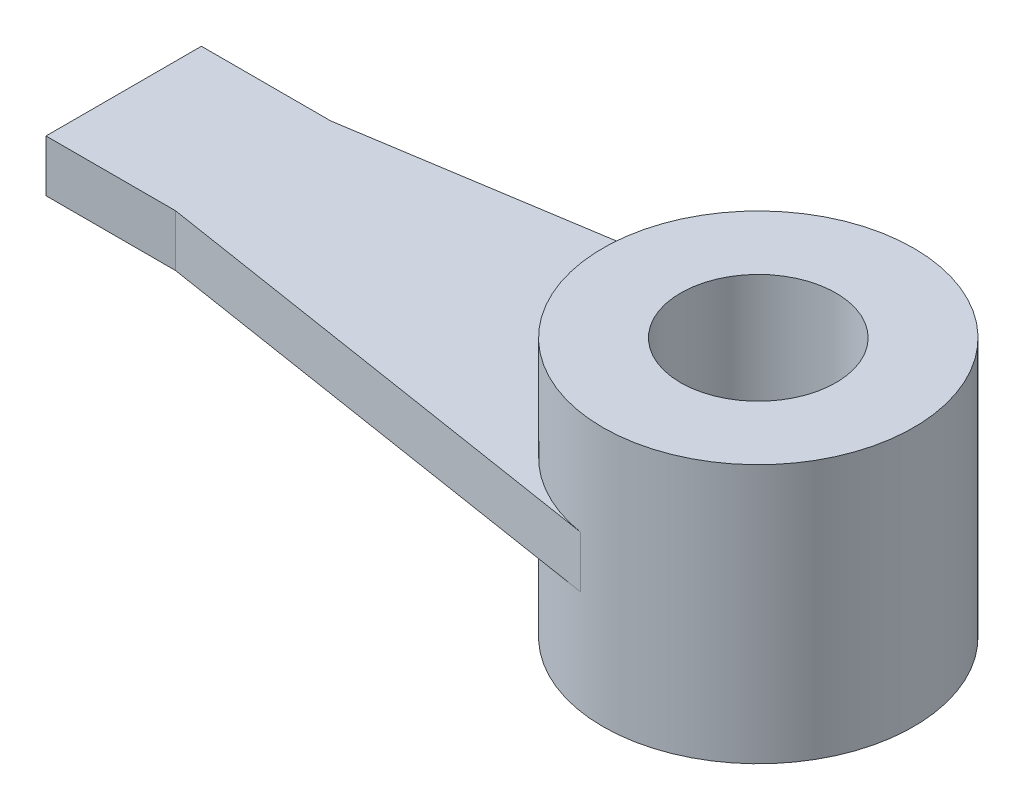
SolidWorks part; units mm, degrees
ref_plane "Front Plane" through (0, 0, 0) normal (0, 0, 1) x (1, 0, 0)
ref_plane "Top Plane" through (0, 0, 0) normal (0, 1, 0) x (1, 0, 0)
ref_plane "Right Plane" through (0, 0, 0) normal (1, 0, 0) x (0, 0, -1)
sketch "Sketch1" plane through (0, 0, 0) normal (0, 1, 0) x (1, 0, 0)
  circle A0 centre (0, 0) radius 15
  circle A1 centre (0, 0) radius 30
  dimension "D1" = 60
  dimension "D2" = 30
extrude "Boss-Extrude1" add sketch "Sketch1" along normal mid plane 50
sketch "Sketch2" plane through (0, 0, 0) normal (0, 1, 0) x (1, 0, 0)
  line L0 (0, 0) -> (-122.5, 0) construction
  line L1 (-122.5, 15) -> (-122.5, -15)
  line L2 (-122.5, -15) -> (-97.5, -15)
  line L3 (-97.5, -15) -> (-4.6717, -29.634)
  line L4 (-97.5, 15) -> (-4.6717, 29.634)
  line L5 (-122.5, 15) -> (-97.5, 15)
  line L7 (-110, -15) -> (-110, 15) construction
  circle A0 centre (0, 0) radius 30 construction
  arc A1 (-4.6717, 29.634) -> (-4.6717, -29.634) centre (0, 0) ccw
  dimension "D1" = 25
  dimension "D2" = 30
  dimension "D3" = 110
extrude "Boss-Extrude2" add sketch "Sketch2" along normal mid plane 10 contours L3 A1 L4 L5 L1 L2
